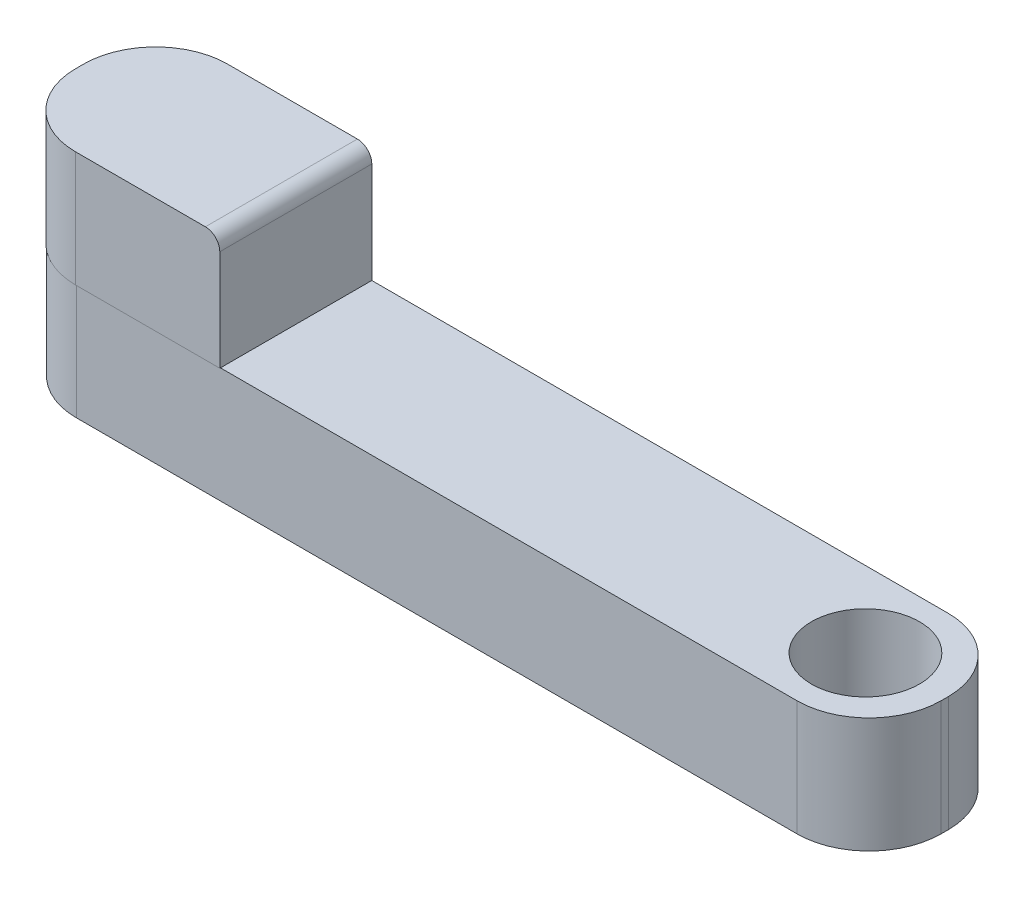
SolidWorks part; units mm, degrees
ref_plane "Front Plane" through (0, 0, 0) normal (0, 0, 1) x (1, 0, 0)
ref_plane "Top Plane" through (0, 0, 0) normal (0, 1, 0) x (1, 0, 0)
ref_plane "Right Plane" through (0, 0, 0) normal (1, 0, 0) x (0, 0, -1)
sketch "Sketch2" plane through (0, 0, 0) normal (0, 1, 0) x (1, 0, 0)
  line L0 (-300, 0) -> (300, 0) construction
  line L1 (-300, 52.5) -> (300, 52.5)
  line L2 (-300, 52.5) -> (-300, -52.5)
  line L3 (-300, -52.5) -> (300, -52.5)
  line L4 (300, 52.5) -> (300, -52.5)
  line L5 (-300, 52.5) -> (300, -52.5) construction
  line L6 (-300, -52.5) -> (300, 52.5) construction
  circle A0 centre (-245, 0) radius 50
  circle A1 centre (245, 0) radius 37.5
  point P0 (0, 0)
  dimension "D4" = 100
  dimension "D6" = 75
  dimension "D1" = 600
  dimension "D2" = 105
  dimension "D3" = 55
  dimension "D5" = 55
extrude "Boss-Extrude2" add sketch "Sketch2" along normal blind 80
sketch "Sketch3" plane through (0, 80, 0) normal (0, 1, 0) x (1, 0, 0)
  line L0 (-300, 52.5) -> (-150, 52.5)
  line L1 (-300, 52.5) -> (-300, -52.9576)
  line L2 (-150, 52.5) -> (-150, -52.9576)
  line L3 (-300, -52.9576) -> (-150, -52.9576)
  line L4 (300, 52.5) -> (-300, 52.5) construction
  dimension "D1" = 150
extrude "Boss-Extrude3" add sketch "Sketch3" along normal blind 80
sketch "Sketch4" plane through (0, 80, 0) normal (0, -1, 0) x (1, 0, 0)
  circle A0 centre (-245.1357, 0) radius 5
  dimension "D1" = 10
extrude "Boss-Extrude4" add sketch "Sketch4" along normal blind 120
fillet "Fillet1" radius 10 1 edges at (-150, 160, 0.2288)
fillet "Fillet3" radius 50 1 edges at (300, 40, 52.5)
fillet "Fillet4" radius 50 1 edges at (300, 40, -52.5)
fillet "Fillet5" radius 50 1 edges at (-300, 40, 52.5)
fillet "Fillet6" radius 50 1 edges at (-300, 120, 52.9576)
fillet "Fillet7" radius 50 1 edges at (-300, 80, -52.5)
